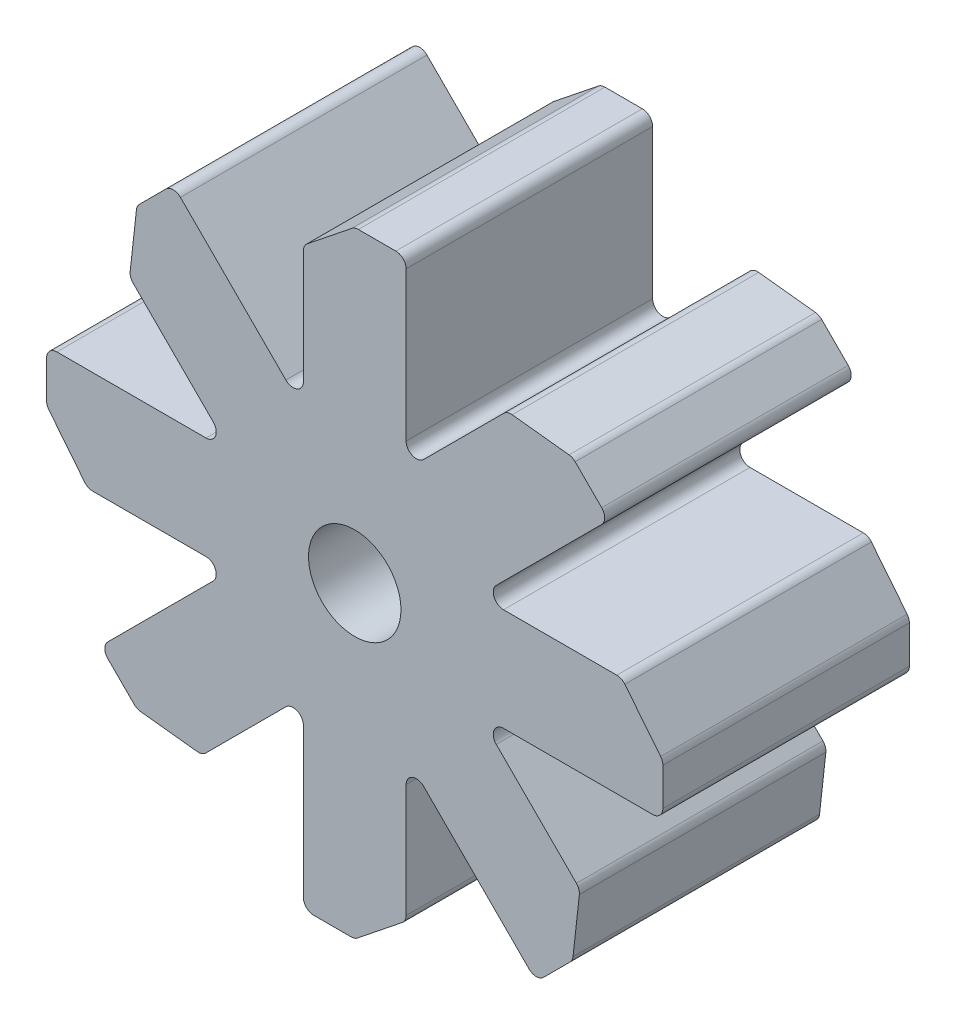
SolidWorks part; units mm, degrees
ref_plane "Front Plane" through (0, 0, 0) normal (0, 0, 1) x (1, 0, 0)
ref_plane "Top Plane" through (0, 0, 0) normal (0, 1, 0) x (1, 0, 0)
ref_plane "Right Plane" through (0, 0, 0) normal (1, 0, 0) x (0, 0, -1)
sketch "Sketch3" plane through (0, 0, 0) normal (0, 0, 1) x (1, 0, 0)
  line L0 (0, -15) -> (0, 15) construction
  line L1 (-15, 0) -> (15, 0) construction
  line L2 (-10.6066, 10.6066) -> (10.6066, -10.6066) construction
  line L3 (-10.6066, -10.6066) -> (10.6066, 10.6066) construction
  line L4 (-2.5, 15) -> (2.5, 15)
  line L5 (15, 2.5) -> (15, -2.5)
  line L6 (8.8388, 12.3744) -> (12.3744, 8.8388)
  line L7 (2.5, 15) -> (2.5, 6.0355)
  line L8 (8.8388, 12.3744) -> (2.5, 6.0355)
  line L9 (12.3744, 8.8388) -> (6.0355, 2.5)
  line L10 (15, 2.5) -> (6.0355, 2.5)
  line L11 (15, -2.5) -> (6.0355, -2.5)
  line L12 (12.3744, -8.8388) -> (6.0355, -2.5)
  line L13 (8.8388, -12.3744) -> (12.3744, -8.8388)
  line L14 (8.8388, -12.3744) -> (2.5, -6.0355)
  line L15 (2.5, -15) -> (2.5, -6.0355)
  line L16 (-2.5, -15) -> (2.5, -15)
  line L17 (-2.5, -15) -> (-2.5, -6.0355)
  line L18 (-8.8388, -12.3744) -> (-2.5, -6.0355)
  line L19 (-8.8388, -12.3744) -> (-12.3744, -8.8388)
  line L20 (-12.3744, -8.8388) -> (-6.0355, -2.5)
  line L21 (-15, -2.5) -> (-6.0355, -2.5)
  line L22 (-15, 2.5) -> (-6.0355, 2.5)
  line L23 (-12.3744, 8.8388) -> (-6.0355, 2.5)
  line L24 (-8.8388, 12.3744) -> (-2.5, 6.0355)
  line L25 (-2.5, 15) -> (-2.5, 6.0355)
  line L26 (-8.8388, 12.3744) -> (-12.3744, 8.8388)
  line L27 (-15, 2.5) -> (-15, -2.5)
  circle A0 centre (0, 0) radius 2.25
  dimension "D1" = 4.5
  dimension "D2" = 45
  dimension "D3" = 45
  dimension "D4" = 15
  dimension "D5" = 5
extrude "Boss-Extrude1" add sketch "Sketch3" along normal blind 12
fillet "Inner Edges" radius 0.5 8 edges at (2.5, 6.0355, 6) (6.0355, 2.5, 6) (6.0355, -2.5, 6) (2.5, -6.0355, 6) (-2.5, -6.0355, 6) (-6.0355, -2.5, 6) (-6.0355, 2.5, 6) (-2.5, 6.0355, 6)
sketch "Sketch4" plane through (0, 0, 12) normal (0, 0, 1) x (1, 0, 0)
  line L0 (2.5, -15) -> (2.5, -13)
  line L1 (2.5, -15) -> (2.5, -7.2426) construction
  line L2 (2.5, -13) -> (2.5, -15)
  line L3 (2.5, -13) -> (0, -15)
  line L4 (-2.5, -15) -> (2.5, -15) construction
  line L5 (-10.6066, -10.6066) -> (-7.4246, -10.9602)
  line L7 (-12.3744, -8.8388) -> (-8.8388, -12.3744) construction
  line L10 (10.6066, -10.6066) -> (12.3744, -8.8388)
  line L11 (8.8388, -12.3744) -> (12.3744, -8.8388) construction
  line L12 (12.3744, -8.8388) -> (10.9602, -7.4246)
  line L13 (12.3744, -8.8388) -> (6.8891, -3.3536) construction
  line L14 (10.9602, -7.4246) -> (10.6066, -10.6066)
  line L15 (0, -15) -> (2.5, -15)
  line L16 (-8.8388, -12.3744) -> (-3.3536, -6.8891) construction
  line L17 (-7.4246, -10.9602) -> (-8.8388, -12.3744)
  line L18 (-8.8388, -12.3744) -> (-10.6066, -10.6066)
  line L19 (-15, 0) -> (-15, -2.5)
  line L20 (-15, 2.5) -> (-15, -2.5) construction
  line L21 (-15, -2.5) -> (-13, -2.5)
  line L22 (-15, -2.5) -> (-7.2426, -2.5) construction
  line L23 (-13, -2.5) -> (-15, 0)
  line L24 (-10.6066, 10.6066) -> (-12.3744, 8.8388)
  line L25 (-8.8388, 12.3744) -> (-12.3744, 8.8388) construction
  line L26 (-12.3744, 8.8388) -> (-10.9602, 7.4246)
  line L27 (-12.3744, 8.8388) -> (-6.8891, 3.3536) construction
  line L28 (-10.9602, 7.4246) -> (-10.6066, 10.6066)
  line L29 (0, 15) -> (-2.5, 15)
  line L30 (2.5, 15) -> (-2.5, 15) construction
  line L31 (-2.5, 15) -> (-2.5, 13)
  line L32 (-2.5, 15) -> (-2.5, 7.2426) construction
  line L33 (-2.5, 13) -> (0, 15)
  line L34 (7.4246, 10.9602) -> (8.8388, 12.3744)
  line L35 (8.8388, 12.3744) -> (3.3536, 6.8891) construction
  line L36 (8.8388, 12.3744) -> (10.6066, 10.6066)
  line L37 (12.3744, 8.8388) -> (8.8388, 12.3744) construction
  line L38 (10.6066, 10.6066) -> (7.4246, 10.9602)
  line L39 (15, 0) -> (15, 2.5)
  line L40 (15, -2.5) -> (15, 2.5) construction
  line L41 (15, 2.5) -> (13, 2.5)
  line L42 (15, 2.5) -> (7.2426, 2.5) construction
  line L43 (13, 2.5) -> (15, 0)
  line M21 (8.8388, 12.3744) -> (3.3536, 6.8891)
  line M24 (2.5, 15) -> (-2.5, 15)
  line M25 (-2.5, 15) -> (-2.5, 7.2426)
  line M28 (-8.8388, 12.3744) -> (-12.3744, 8.8388)
  line M29 (-12.3744, 8.8388) -> (-6.8891, 3.3536)
  line M32 (-15, 2.5) -> (-15, -2.5)
  line M33 (-15, -2.5) -> (-7.2426, -2.5)
  line M36 (-12.3744, -8.8388) -> (-8.8388, -12.3744)
  line M37 (-8.8388, -12.3744) -> (-3.3536, -6.8891)
  line M40 (-2.5, -15) -> (2.5, -15)
  line M41 (2.5, -15) -> (2.5, -7.2426)
  line M44 (8.8388, -12.3744) -> (12.3744, -8.8388)
  line M45 (12.3744, -8.8388) -> (6.8891, -3.3536)
  line M48 (15, -2.5) -> (15, 2.5)
  line M49 (15, 2.5) -> (7.2426, 2.5)
  line M52 (12.3744, 8.8388) -> (8.8388, 12.3744)
  dimension "D1" = 2
extrude "Cut-Extrude2" cut sketch "Sketch4" against normal through all contours L14 M45 M44 | L43 M49 M48 | L38 M52 M21 | L33 M25 M24 | L28 M29 M28 | L23 M33 M32 | L5 M36 M37 | L3 M41 M40
fillet "Outer Edges" radius 0.5 24 edges at (10.9602, -7.4246, 6) (10.6066, -10.6066, 6) (8.8388, -12.3744, 6) (2.5, -13, 6) (0, -15, 6) (-2.5, -15, 6) (-7.4246, -10.9602, 6) (-10.6066, -10.6066, 6) (-12.3744, -8.8388, 6) (-13, -2.5, 6) (-15, 0, 6) (-15, 2.5, 6) (-10.9602, 7.4246, 6) (-10.6066, 10.6066, 6) (-8.8388, 12.3744, 6) (-2.5, 13, 6) (0, 15, 6) (2.5, 15, 6) (7.4246, 10.9602, 6) (10.6066, 10.6066, 6) (12.3744, 8.8388, 6) (15, -2.5, 6) (13, 2.5, 6) (15, 0, 6)
